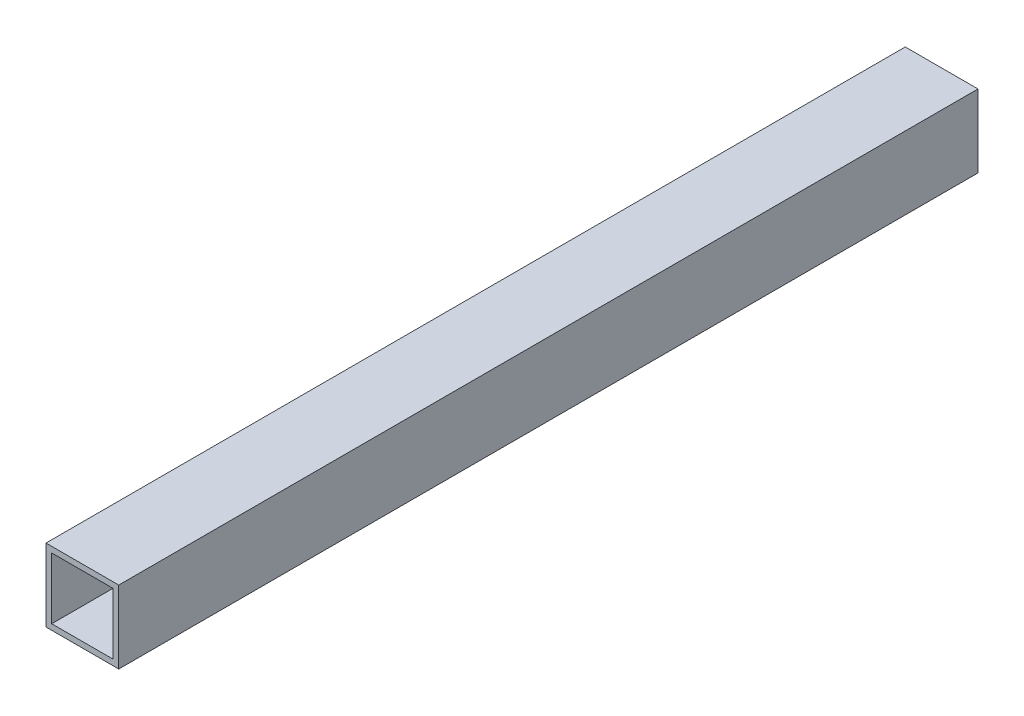
SolidWorks part; units mm, degrees
ref_plane "Front Plane" through (0, 0, 0) normal (0, 0, 1) x (1, 0, 0)
ref_plane "Top Plane" through (0, 0, 0) normal (0, 1, 0) x (1, 0, 0)
ref_plane "Right Plane" through (0, 0, 0) normal (1, 0, 0) x (0, 0, -1)
sketch "Sketch1" plane through (0, 0, 0) normal (0, 0, 1) x (1, 0, 0)
  line L0 (-10.7, 10.7) -> (10.7, 10.7)
  line L1 (-12.7, -12.7) -> (12.7, -12.7)
  line L2 (-12.7, -12.7) -> (-12.7, 12.7)
  line L3 (-12.7, 12.7) -> (12.7, 12.7)
  line L4 (12.7, -12.7) -> (12.7, 12.7)
  line L5 (-12.7, -12.7) -> (12.7, 12.7) construction
  line L6 (-12.7, 12.7) -> (12.7, -12.7) construction
  line L7 (10.7, -10.7) -> (10.7, 10.7)
  line L8 (-10.7, -10.7) -> (10.7, -10.7)
  line L9 (-10.7, -10.7) -> (-10.7, 10.7)
  point P0 (0, 0)
  dimension "D1" = 25.4
  dimension "D2" = 2
extrude "Boss-Extrude1" add sketch "Sketch1" along normal blind 300
